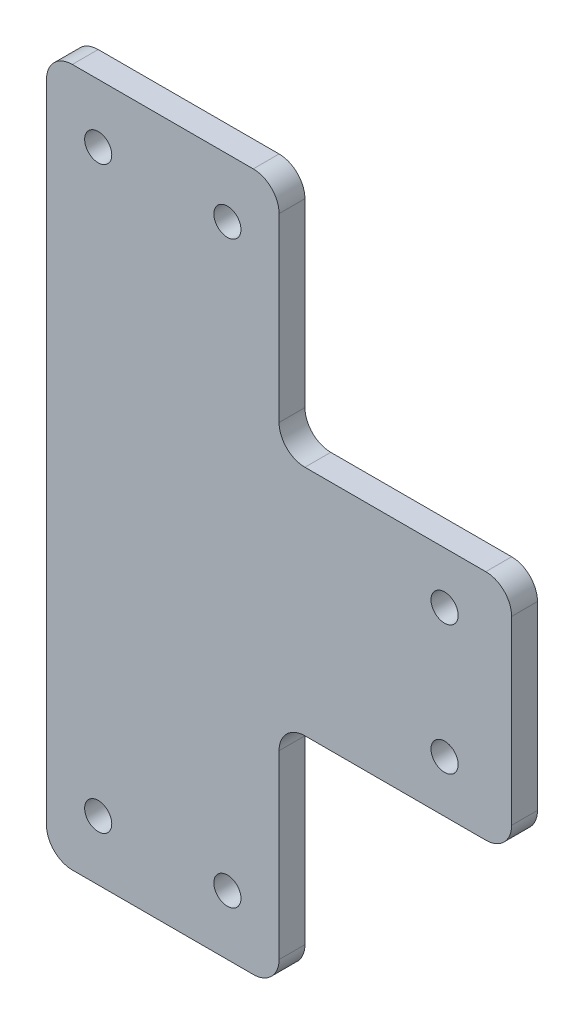
SolidWorks part; units mm, degrees
ref_plane "Front Plane" through (0, 0, 0) normal (0, 0, 1) x (1, 0, 0)
ref_plane "Top Plane" through (0, 0, 0) normal (0, 1, 0) x (1, 0, 0)
ref_plane "Right Plane" through (0, 0, 0) normal (1, 0, 0) x (0, 0, -1)
sketch "Sketch1" plane through (0, 0, 0) normal (0, 0, 1) x (1, 0, 0)
  line L0 (0, -18) -> (0, -54)
  line L1 (-36, 54) -> (0, 54)
  line L2 (-36, 54) -> (-36, -54)
  line L3 (-36, -54) -> (0, -54)
  line L4 (0, 54) -> (0, 18)
  line L5 (0, 18) -> (36, 18)
  line L7 (0, -18) -> (36, -18)
  line L8 (36, 18) -> (36, -18)
  dimension "D1" = 108
  dimension "D2" = 36
  dimension "D3" = 36
  dimension "D4" = 36
  dimension "D5" = 18
  dimension "D6" = 36
  dimension "D7" = 36
extrude "Boss-Extrude1" add sketch "Sketch1" along normal blind 4
hole_wizard "M5x0.8 Tapped Hole1" positions "Sketch3" profile "Sketch2" tap size "M5x0.8" standard "ANSI Metric" end condition through all
sketch "Sketch3" plane through (0, 0, 4) normal (0, 0, 1) x (1, 0, 0)
  point P0 (-28, 44.9124)
  point P2 (-8, 44.9124)
  point P4 (25.6168, 10)
  point P6 (25.6168, -10)
  point P8 (-28, -44.758)
  point P10 (-8, -44.758)
  dimension "D1" = 20
  dimension "D2" = 20
  dimension "D3" = 20
  dimension "D4" = 8
  dimension "D5" = 10
  dimension "D6" = 8
sketch "Sketch2" plane through (-28, 44.9124, 4) normal (1, 0, 0) x (0, -1, 0)
  line L0 (0, 0) -> (0, 4)
  line L1 (0, 4) -> (2.1, 4)
  line L2 (2.1, 4) -> (2.1, 0)
  line L5 (2.1, 0) -> (0, 0)
  line L11 (0, -6.35) -> (0, 107.95) construction
  dimension "Thru Tap Drill Dia." = 4.2
  dimension "Thru Tap Drill Depth" = 4
cosmetic thread "Hole Thread1"
cosmetic thread "Hole Thread2"
cosmetic thread "Hole Thread3"
cosmetic thread "Hole Thread4"
cosmetic thread "Hole Thread5"
cosmetic thread "Hole Thread6"
fillet "Fillet1" radius 4 8 edges at (-36, -54, 2) (0, -54, 2) (0, -18, 2) (36, -18, 2) (36, 18, 2) (0, 18, 2) (0, 54, 2) (-36, 54, 2)
